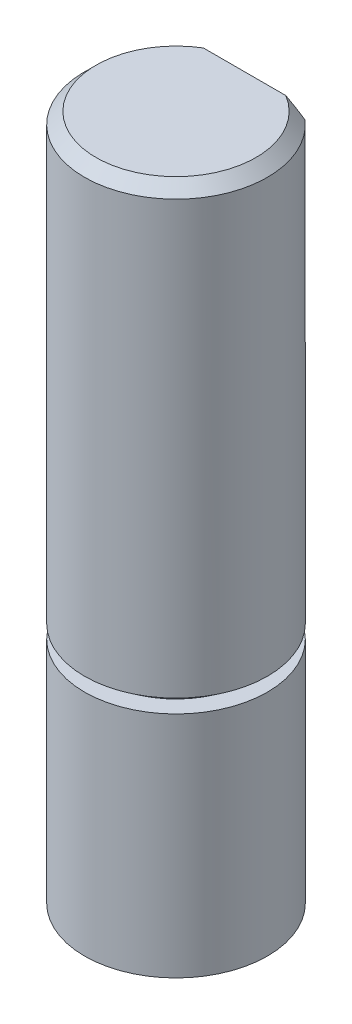
SolidWorks part; units mm, degrees
material "Plain Carbon Steel"
ref_plane "Front" through (0, 0, 0) normal (0, 0, 1) x (1, 0, 0)
ref_plane "Top" through (0, 0, 0) normal (0, 1, 0) x (1, 0, 0)
ref_plane "Right" through (0, 0, 0) normal (1, 0, 0) x (0, 0, -1)
sketch "Sketch1" plane through (0, 0, 0) normal (0, 1, 0) x (1, 0, 0)
  circle A0 centre (0, 0) radius 4
  dimension "D1" = 8
extrude "Boss-Extrude1" add sketch "Sketch1" along normal blind 20 and the other way blind 10
chamfer "Chamfer1" distance 0.5 angle 45 1 edges at (0, 20, 4)
sketch "Sketch2" plane through (0, 20, 0) normal (0, 1, 0) x (1, 0, 0)
  line L0 (-2.6458, 3) -> (2.6458, 3)
  circle A0 centre (0, 0) radius 4 construction
  arc A1 (2.6458, 3) -> (-2.6458, 3) centre (0, 0) ccw
  dimension "D1" = 3
extrude "Cut-Extrude1" cut sketch "Sketch2" against normal blind 12
sketch "Sketch3" plane through (0, 0, 0) normal (1, 0, 0) x (0, 0, -1)
  line L0 (4.9019, 0.6) -> (3.2, 0.6)
  line L1 (3.2, 0.6) -> (3.2, 0)
  line L2 (3.2, 0) -> (4.9019, 0)
  line L3 (4.9019, 0) -> (4.9019, 0.6)
  line L4 (3, 20) -> (-3.5, 20) construction
  line L6 (0, 0) -> (0, 19.7552) construction
  dimension "D1" = 3.2
  dimension "D2" = 0.6
  dimension "D3" = 20
revolve "Cut-Revolve1" cut sketch "Sketch3" angle 360 about L6
